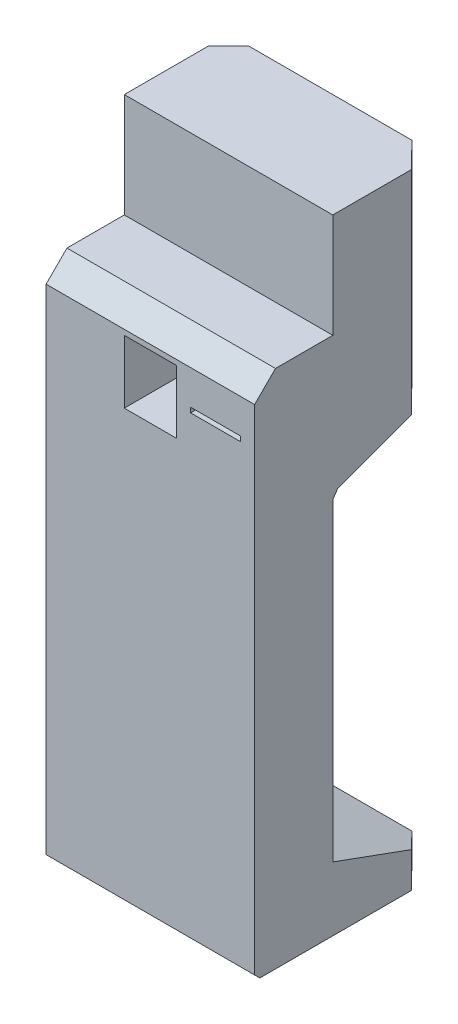
SolidWorks part; units mm, degrees
ref_plane "Front Plane" through (0, 0, 0) normal (0, 0, 1) x (1, 0, 0)
ref_plane "Top Plane" through (0, 0, 0) normal (0, 1, 0) x (1, 0, 0)
ref_plane "Right Plane" through (0, 0, 0) normal (1, 0, 0) x (0, 0, -1)
sketch "Sketch1" plane through (0, 0, 0) normal (1, 0, 0) x (0, 0, -1)
  line L0 (0, 0) -> (-340, 0)
  line L1 (-350, 10) -> (-350, 957.7637)
  line L2 (-310, 997.7637) -> (-200, 997.7637)
  line L3 (-200, 997.7637) -> (-200, 1197.7637)
  line L4 (0, 967.7637) -> (0, 817.7637)
  line L5 (0, 50) -> (-200, 122.794)
  line L6 (-200, 1197.7637) -> (-150, 1197.7637)
  line L7 (-150, 1197.7637) -> (-18, 1021.7637) construction
  line L8 (-310, 997.7637) -> (-350, 957.7637)
  line L9 (-27.4748, 797.7637) -> (-180, 797.7637) construction
  line L10 (-200, 777.7637) -> (-200, 20) construction
  line L11 (-190, 10) -> (0, 10) construction
  line L12 (0, 10) -> (0, 0) construction
  line L13 (-200, 20) -> (-190, 10) construction
  line L14 (-340, 0) -> (-350, 10)
  line L15 (-180, 797.7637) -> (-200, 777.7637) construction
  line L16 (-9.3969, 804.3435) -> (-27.4748, 797.7637)
  line L17 (-27.4748, 797.7637) -> (-190.6031, 738.3898)
  line L18 (-200, 724.9696) -> (-200, 122.794)
  line L19 (0, 997.7637) -> (0, 1197.7637)
  line L20 (0, 1197.7637) -> (-150, 1197.7637)
  line L21 (-18, 1021.7637) -> (0, 967.7637) construction
  line L22 (0, 817.7637) -> (-9.3969, 804.3435)
  line L23 (-190.6031, 738.3898) -> (-200, 724.9696)
  line L24 (0, 997.7637) -> (0, 967.7637)
  line L25 (0, 10) -> (-200, 70) construction
  line L27 (0, 50) -> (0, 0)
  arc A0 (0, 997.7637) -> (-200, 1197.7637) centre (-200, 997.7637) ccw construction
  arc A1 (-350, 957.7637) -> (-310, 997.7637) centre (-310, 957.7637) cw construction
  point P1 (-350, 0)
  point P3 (0, 0)
  point P12 (0, 797.7637)
  point P13 (-200, 797.7637)
  point P15 (-200, 10)
  point P23 (0, 807.7637)
  point P25 (-200, 734.9696)
  point P32 (0, 0)
  point P36 (-150, 999.8015)
  point P37 (0, 0)
  point P38 (0, 1197.7637)
  dimension "D5" = 40
  dimension "D2" = 350
  dimension "D3" = 110
  dimension "D6" = 50
  dimension "D7" = 150
  dimension "D8" = 10
  dimension "D10" = 110
  dimension "D9" = 200
  dimension "D15" = 60
  dimension "D16" = 50
extrude "Boss-Extrude1" add sketch "Sketch1" along normal blind 400
sketch "Sketch2" plane through (0, 0, 350) normal (0, 0, 1) x (1, 0, 0)
  line L0 (200, 947.7637) -> (200, 997.7637) construction
  line L1 (150, 947.7637) -> (250, 947.7637)
  line L2 (150, 947.7637) -> (150, 826.7637)
  line L3 (150, 826.7637) -> (250, 826.7637)
  line L4 (250, 947.7637) -> (250, 826.7637)
  line L5 (400, 997.7637) -> (0, 997.7637) construction
  line L6 (277.35, 887.2637) -> (250, 887.2637) construction
  line L7 (372.65, 891.9637) -> (277.35, 891.9637)
  line L8 (372.65, 891.9637) -> (372.65, 882.5637)
  line L9 (372.65, 882.5637) -> (277.35, 882.5637)
  line L10 (277.35, 891.9637) -> (277.35, 882.5637)
  line L11 (250, 947.7637) -> (400, 947.7637) construction
  line L12 (400, 957.7637) -> (400, 10) construction
  line L13 (325, 947.7637) -> (325, 891.9637) construction
  dimension "D1" = 121
  dimension "D2" = 100
  dimension "D3" = 50
  dimension "D4" = 9.4
  dimension "D5" = 95.3
extrude "Cut-Extrude1" cut sketch "Sketch2" against normal blind 268
sketch "Sketch3" plane through (0, 0, 0) normal (0, -1, 0) x (-1, 0, 0)
  line L0 (32.9719, -72.8044) -> (-67.7282, 29.5696)
  line L1 (-67.7282, 29.5696) -> (-322.6486, 29.5696)
  line L2 (-322.6486, 29.5696) -> (-423.3487, -72.8044)
  line L3 (-423.3487, -72.8044) -> (-423.3487, 100.0695)
  line L4 (-423.3487, 100.0695) -> (32.9719, 100.0695)
  line L5 (32.9719, 100.0695) -> (32.9719, -72.8044)
  line L6 (-195.1884, 29.5696) -> (-195.1884, -2.4875) construction
  line L8 (-195.1884, 29.5696) -> (-195.1884, 100.0695) construction
extrude "Cut-Extrude2" cut sketch "Sketch3" against normal through all both and the other way through all
